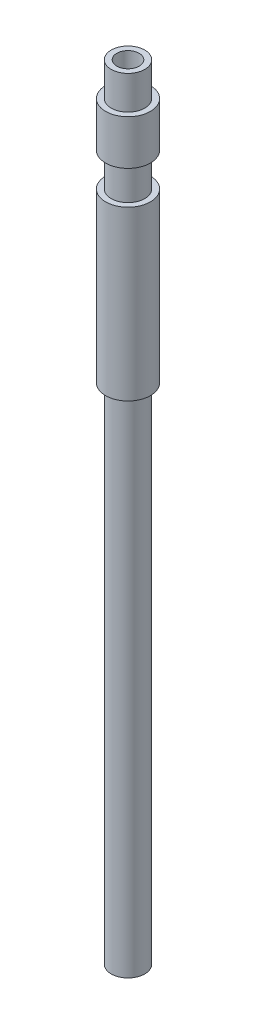
SolidWorks part; units mm, degrees
material "Простая углеродистая сталь"
ref_plane "Спереди" through (0, 0, 0) normal (0, 0, 1) x (1, 0, 0)
ref_plane "Сверху" through (0, 0, 0) normal (0, 1, 0) x (1, 0, 0)
ref_plane "Справа" through (0, 0, 0) normal (1, 0, 0) x (0, 0, -1)
sketch "Эскиз1" plane through (0, 0, 0) normal (0, 1, 0) x (1, 0, 0)
  circle A0 centre (0, 0) radius 1
  circle A1 centre (0, 0) radius 2
  dimension "D1" = 4
  dimension "D2" = 2
extrude "Бобышка-Вытянуть1" add sketch "Эскиз1" along normal blind 70
sketch "Эскиз2" plane through (0, 0, 0) normal (0, 0, 1) x (1, 0, 0)
  line L0 (2, 70) -> (1.5, 70)
  line L1 (2, 70) -> (2, 67)
  line L2 (1.5, 70) -> (1.5, 67)
  line L3 (2, 67) -> (1.5, 67)
  line L4 (2, 63) -> (1.5, 63)
  line L5 (2, 63) -> (2, 60)
  line L6 (1.5, 63) -> (1.5, 60)
  line L7 (2, 60) -> (1.5, 60)
  line L8 (1, 70) -> (-1, 70) construction
  line L9 (1, 70) -> (-1, 70) construction
  line L10 (0, 70) -> (0, 0) construction
  line L11 (-2, 0) -> (2, 0) construction
  line L12 (-2, 0) -> (2, 0) construction
  dimension "D1" = 3
  dimension "D2" = 0.5
  dimension "D3" = 2
  dimension "D4" = 7
revolve "Вырез-Повернуть1" cut sketch "Эскиз2" angle 360 about L10
sketch "Эскиз3" plane through (0, 0, 0) normal (0, 0, 1) x (1, 0, 0)
  line L0 (2, 0) -> (1.5, 0)
  line L1 (2, 0) -> (2, 45)
  line L2 (1.5, 0) -> (1.5, 45)
  line L3 (2, 45) -> (1.5, 45)
  line L4 (2, 60) -> (-2, 60) construction
  line L5 (0, 0) -> (0, 70) construction
  line L6 (1, 70) -> (-1, 70) construction
  line L7 (1, 70) -> (-1, 70) construction
  dimension "D1" = 15
  dimension "D2" = 0.5
revolve "Вырез-Повернуть2" cut sketch "Эскиз3" angle 360 about L5
sketch "Эскиз4" plane through (0, 0, 0) normal (0, 0, 1) x (1, 0, 0)
  line L0 (-2, 50) -> (2, 50) construction
  line L1 (1.5, 70) -> (-1.5, 70) construction
  line L2 (1.5, 70) -> (-1.5, 70) construction
  line L3 (2, 60) -> (-2, 60) construction
  line L4 (2, 60) -> (-2, 60) construction
  line L5 (-2, 60) -> (-2, 45) construction
  line L6 (2, 45) -> (2, 60) construction
  dimension "D1" = 20
ref_plane "Плоскость1" through (0, 50, 0) normal (0, 1, 0) x (1, 0, 0)
sketch "Эскиз5" plane through (0, 50, 0) normal (0, 1, 0) x (1, 0, 0)
  line L0 (-2, 0) -> (2, 0) construction
  circle A0 centre (0, 0) radius 2 construction
